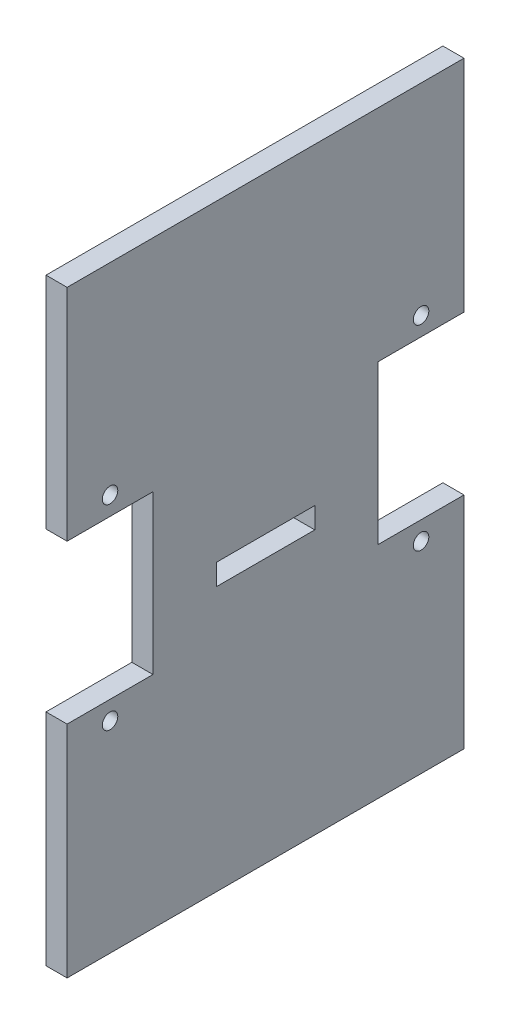
SolidWorks part; units mm, degrees
ref_plane "Front Plane" through (0, 0, 0) normal (0, 0, 1) x (1, 0, 0)
ref_plane "Top Plane" through (0, 0, 0) normal (0, 1, 0) x (1, 0, 0)
ref_plane "Right Plane" through (0, 0, 0) normal (1, 0, 0) x (0, 0, -1)
sketch "Sketch1" plane through (0, 0, 0) normal (1, 0, 0) x (0, 0, -1)
  line L0 (30.1, 0) -> (-30.1, 0) construction
  line L1 (-28.2, -42.5) -> (28.2, -42.5)
  line L2 (-28.2, -42.5) -> (-28.2, -11.25)
  line L3 (-28.2, 42.5) -> (28.2, 42.5)
  line L4 (28.2, -42.5) -> (28.2, -11.25)
  line L5 (-28.2, -42.5) -> (28.2, 42.5) construction
  line L6 (-28.2, 42.5) -> (28.2, -42.5) construction
  line L7 (0, 0) -> (16, 0) construction
  line L8 (28.2, -11.25) -> (16, -11.25)
  line L9 (-28.2, 11.25) -> (-28.2, 42.5)
  line L10 (28.2, 11.25) -> (16, 11.25)
  line L11 (16, -11.25) -> (16, 11.25)
  line L12 (22.1, 11.25) -> (22.1, 13.9) construction
  line L13 (0, 42.5) -> (0, -42.5) construction
  line L14 (-28.2, -11.25) -> (-16, -11.25)
  line L15 (-16, -11.25) -> (-16, 11.25)
  line L16 (28.2, 11.25) -> (28.2, 42.5)
  line L17 (-28.2, 11.25) -> (-16, 11.25)
  circle A0 centre (22.1, 13.9) radius 1.1
  circle A1 centre (22.1, -13.9) radius 1.1
  circle A2 centre (-22.1, -13.9) radius 1.1
  circle A3 centre (-22.1, 13.9) radius 1.1
  point P0 (0, 0)
  point P10 (22.1, 11.25)
  dimension "D6" = 2.2
  dimension "D3" = 85
  dimension "D4" = 56.4
  dimension "D5" = 16
  dimension "D7" = 2.65
extrude "Boss-Extrude1" add sketch "Sketch1" along normal blind 3
sketch "Sketch2" plane through (3, 0, 0) normal (1, 0, 0) x (0, 0, -1)
  line L0 (-16, 11.25) -> (16, 11.25) construction
  line L1 (0, 11.25) -> (0, -1.95) construction
  line L4 (-7, -1.95) -> (7, -1.95)
  line L5 (-7, -1.95) -> (-7, -4.95)
  line L6 (-7, -4.95) -> (7, -4.95)
  line L8 (7, -1.95) -> (7, -4.95)
  point P11 (0, -1.95)
  dimension "D1" = 13.2
  dimension "D2" = 14
  dimension "D3" = 3
extrude "Cut-Extrude1" cut sketch "Sketch2" against normal blind 3
